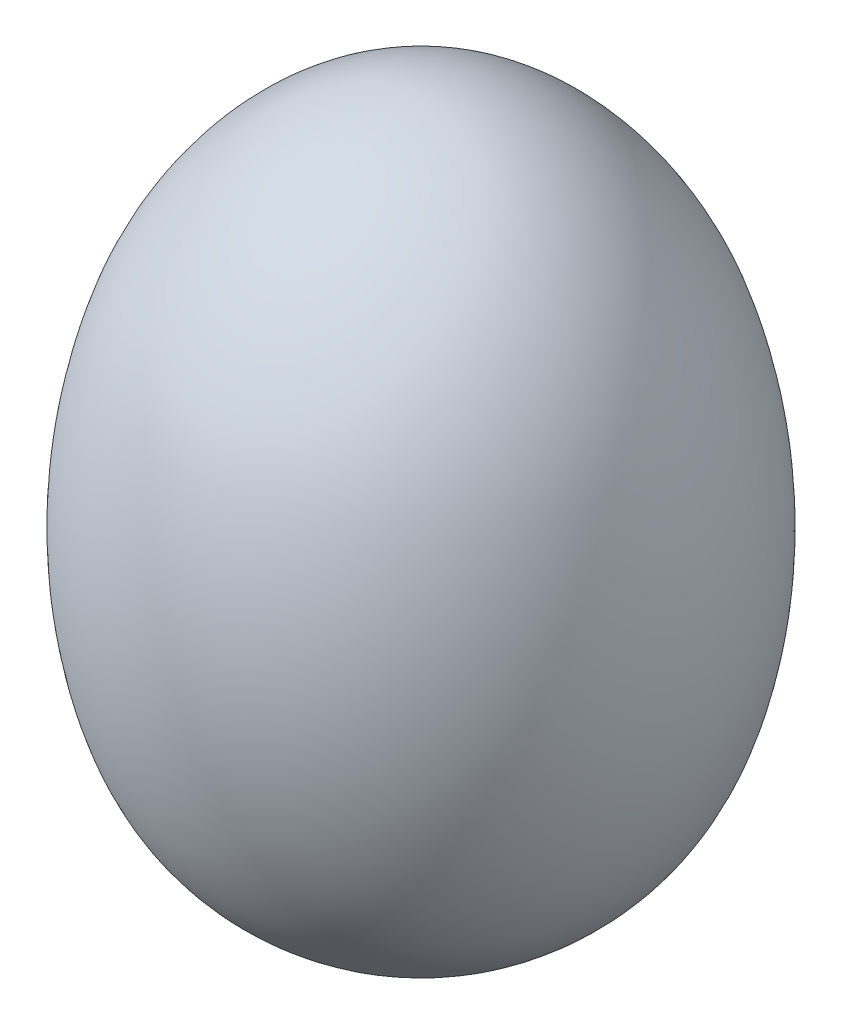
SolidWorks part; units mm, degrees
ref_plane "Front Plane" through (0, 0, 0) normal (0, 0, 1) x (1, 0, 0)
ref_plane "Top Plane" through (0, 0, 0) normal (0, 1, 0) x (1, 0, 0)
ref_plane "Right Plane" through (0, 0, 0) normal (1, 0, 0) x (0, 0, -1)
sketch "Sketch1" plane through (0, 0, 0) normal (0, 0, 1) x (1, 0, 0)
  line L0 (6.123, -92.149) -> (-51.8698, -91.2342) construction
  line L3 (0, 58.2421) -> (0, 0)
  spline S0 degree 3 poles (0, 0) (-6.8044, 0.1781) (-16.4851, 5.7718) (-22.5275, 22.4238) (-21.8442, 34.3384) (-16.6272, 49.9901) (-8.9886, 58.2023) (0, 58.2421) knots 0 0 0 0 0.246781 0.376034 0.652336 0.673977 1 1 1 1
  dimension "D1" = 58
  dimension "D2" = 58.2421
revolve "Revolve1" add sketch "Sketch1" angle 360 about L3
